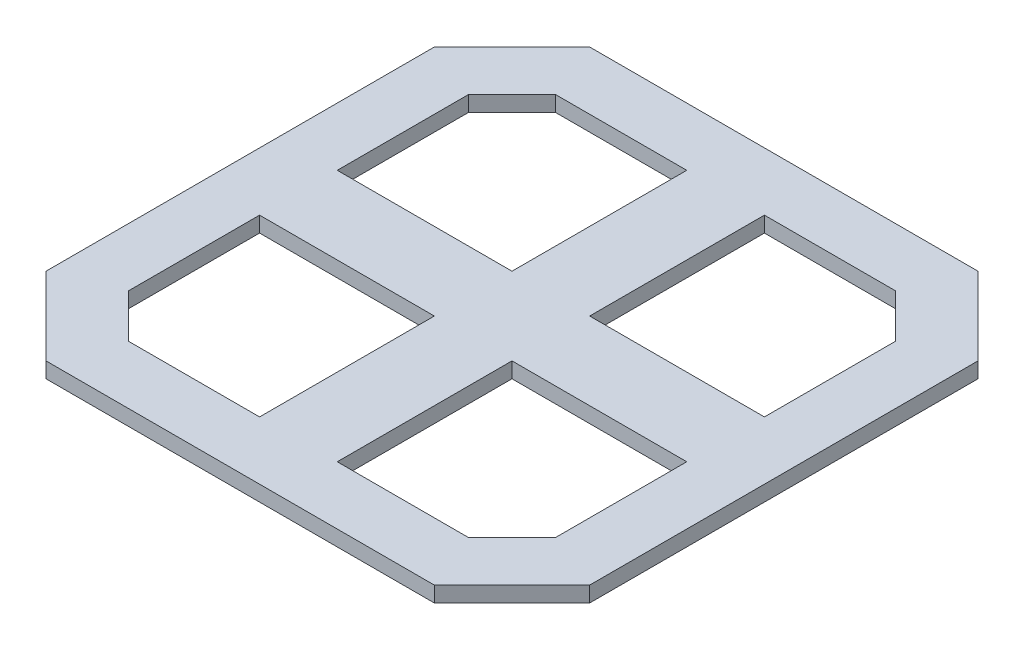
SolidWorks part; units mm, degrees
material "Thornel VCB-20 Carbon Cloth"
ref_plane "Front Plane" through (0, 0, 0) normal (0, 0, 1) x (1, 0, 0)
ref_plane "Top Plane" through (0, 0, 0) normal (0, 1, 0) x (1, 0, 0)
ref_plane "Right Plane" through (0, 0, 0) normal (1, 0, 0) x (0, 0, -1)
sketch "Sketch2" plane through (0, 0, 0) normal (0, 1, 0) x (1, 0, 0)
  line L1 (-35, 35) -> (35, 35)
  line L2 (-35, 35) -> (-35, -35)
  line L3 (-35, -35) -> (35, -35)
  line L4 (35, 35) -> (35, -35)
  line L5 (-35, 35) -> (35, -35) construction
  line L6 (-35, -35) -> (35, 35) construction
  point P0 (0, 0)
  dimension "D1" = 70
  dimension "D2" = 70
extrude "Boss-Extrude1" add sketch "Sketch2" along normal blind 2
sketch "Sketch4" plane through (0, 0, 0) normal (0, -1, 0) x (1, 0, 0)
  line L0 (25, 35) -> (35, 25)
  line L1 (-35, 35) -> (35, 35) construction
  line L2 (35, 35) -> (35, -35) construction
  line L3 (25, 35) -> (35, 35)
  line L4 (35, 35) -> (35, 25)
  line L5 (0, 0) -> (1.77, 0) construction
  line L6 (21.8934, 27.5) -> (27.5, 21.8934)
  line L7 (27.5, 21.8934) -> (27.5, 5)
  line L8 (27.5, 5) -> (5, 5)
  line L9 (5, 5) -> (5, 27.5)
  line L10 (5, 27.5) -> (21.8934, 27.5)
  line L11 (0, -35) -> (0, 35) construction
  line L12 (35, -35) -> (-35, -35) construction
  line L13 (-35, 0) -> (35, 0) construction
  line L14 (-35, -35) -> (-35, 35) construction
  dimension "D1" = 45
  dimension "D2" = 7.5
  dimension "D3" = 7.5
  dimension "D4" = 5
  dimension "D5" = 5
  dimension "D6" = 7.5
  dimension "D7" = 25
extrude "Cut-Extrude1" cut sketch "Sketch4" against normal up to surface (2 mm away) up to face at (0, 2, 0)
sketch "Sketch5" plane through (0, 0, 0) normal (1, 0, 0) x (0, 0, -1)
  line L0 (0, -0.174) -> (0, 0.9435) construction
pattern_circular "CirPattern1" count 4 over 360 about axis through (0, 0, 0) along (0, 1, 0) of "Cut-Extrude1"
sketch "Sketch6" plane through (0, 2, 0) normal (0, 1, 0) x (1, 0, 0)
  line L0 (30, -30) -> (-30, 30) construction
  line L1 (25, -35) -> (35, -25) construction
  line L2 (-25, 35) -> (-35, 25) construction
  line L3 (-30, -30) -> (30, 30) construction
  line L4 (-35, -25) -> (-25, -35) construction
  line L5 (35, 25) -> (25, 35) construction
